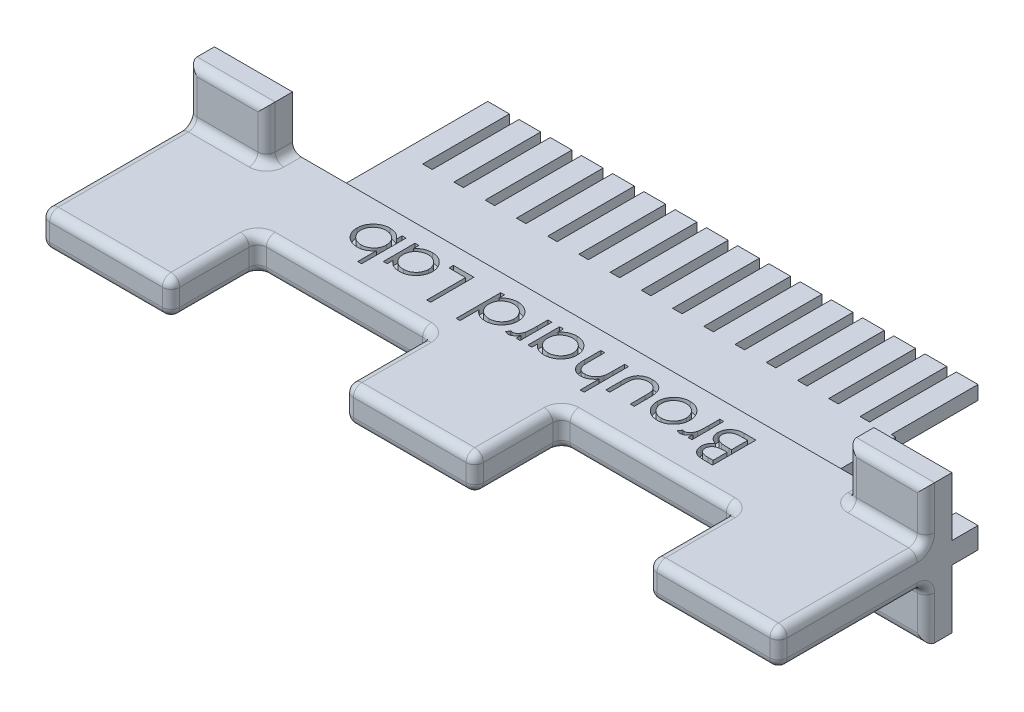
SolidWorks part; units mm, degrees
ref_plane "Front Plane" through (0, 0, 0) normal (0, 0, 1) x (1, 0, 0)
ref_plane "Top Plane" through (0, 0, 0) normal (0, 1, 0) x (1, 0, 0)
ref_plane "Right Plane" through (0, 0, 0) normal (1, 0, 0) x (0, 0, -1)
sketch "Sketch1" plane through (0, 0, 0) normal (0, 0, 1) x (1, 0, 0)
  line L1 (-42.5, 2) -> (42.5, 2)
  line L2 (-42.5, 2) -> (-42.5, -2)
  line L3 (-42.5, -2) -> (42.5, -2)
  line L4 (42.5, 2) -> (42.5, -2)
  line L5 (-42.5, 2) -> (42.5, -2) construction
  line L6 (-42.5, -2) -> (42.5, 2) construction
  point P0 (0, 0)
  dimension "D1" = 85
  dimension "D2" = 4
extrude "Boss-Extrude1" add sketch "Sketch1" along normal blind 10
sketch "Sketch2" plane through (0, 0, 10) normal (0, 0, 1) x (1, 0, 0)
  line L0 (-42.5, -2) -> (42.5, -2) construction
  line L1 (-42.5, 2) -> (-27.5, 2)
  line L2 (-42.5, 2) -> (-42.5, -2)
  line L3 (-42.5, -2) -> (-27.5, -2)
  line L4 (-27.5, 2) -> (-27.5, -2)
  line L6 (42.5, 2) -> (27.5, 2)
  line L7 (42.5, 2) -> (42.5, -2)
  line L8 (42.5, -2) -> (27.5, -2)
  line L9 (27.5, 2) -> (27.5, -2)
  line L10 (-7.5, 2) -> (7.5, 2)
  line L11 (-7.5, 2) -> (-7.5, -2)
  line L12 (-7.5, -2) -> (7.5, -2)
  line L13 (7.5, 2) -> (7.5, -2)
  line L14 (-7.5, 2) -> (7.5, -2) construction
  line L15 (-7.5, -2) -> (7.5, 2) construction
  point P12 (0, 0)
  dimension "D1" = 15
extrude "Boss-Extrude2" add sketch "Sketch2" along normal blind 10
sketch "Sketch3" plane through (0, 0, 0) normal (0, 0, -1) x (-1, 0, 0)
  line L9 (42.5, -1.225) -> (39.95, -1.225)
  line L10 (42.5, -1.225) -> (42.5, 1.225)
  line L11 (42.5, 1.225) -> (39.95, 1.225)
  line L12 (39.95, -1.225) -> (39.95, 1.225)
  line L13 (42.5, -1.225) -> (39.95, 1.225) construction
  line L14 (42.5, 1.225) -> (39.95, -1.225) construction
  line L15 (42.5, 2) -> (42.5, -2) construction
  line L16 (0, 0) -> (0, 13.9589)
  line L17 (-42.5, 1.225) -> (-39.95, -1.225) construction
  line L18 (-42.5, -1.225) -> (-39.95, 1.225) construction
  line L19 (-39.95, -1.225) -> (-39.95, 1.225)
  line L20 (-42.5, 1.225) -> (-39.95, 1.225)
  line L21 (-42.5, -1.225) -> (-42.5, 1.225)
  line L22 (-42.5, -1.225) -> (-39.95, -1.225)
  point P3 (42.5, 0)
  point P10 (41.225, 0)
  point P16 (-41.225, 0)
  line M3 (-42.5, 2) -> (-42.5, -2)
  dimension "D1" = 2.45
  dimension "D2" = 2.55
extrude "Boss-Extrude3" add sketch "Sketch3" along normal blind 3 contours L22 L19 L20 M3 | L12 L11 L10 L9
sketch "Sketch4" plane through (0, 0, 0) normal (0, 0, -1) x (-1, 0, 0)
  line L1 (28.5, -0.8) -> (-28.5, -0.8)
  line L2 (28.5, -0.8) -> (28.5, 0.8)
  line L3 (28.5, 0.8) -> (-28.5, 0.8)
  line L4 (-28.5, -0.8) -> (-28.5, 0.8)
  line L5 (28.5, -0.8) -> (-28.5, 0.8) construction
  line L6 (28.5, 0.8) -> (-28.5, -0.8) construction
  point P0 (0, 0)
  dimension "D1" = 1.6
  dimension "D2" = 57
extrude "Boss-Extrude4" add sketch "Sketch4" along normal blind 7.5
sketch "Sketch6" plane through (0, 0, 0) normal (0, 0, -1) x (-1, 0, 0)
  line L1 (42.5, -2) -> (33.5, -2)
  line L2 (42.5, -2) -> (42.5, -8)
  line L3 (42.5, -8) -> (33.5, -8)
  line L4 (33.5, -2) -> (33.5, -8)
  line L5 (42.5, 2) -> (33.5, 2)
  line L6 (42.5, 2) -> (42.5, 8)
  line L7 (42.5, 8) -> (33.5, 8)
  line L8 (33.5, 2) -> (33.5, 8)
  line L9 (-42.5, -2) -> (-33.5, -2)
  line L10 (-42.5, -2) -> (-42.5, -8)
  line L11 (-42.5, -8) -> (-33.5, -8)
  line L12 (-33.5, -2) -> (-33.5, -8)
  line L13 (-42.5, 2) -> (-33.5, 2)
  line L14 (-42.5, 2) -> (-42.5, 8)
  line L15 (-42.5, 8) -> (-33.5, 8)
  line L16 (-33.5, 2) -> (-33.5, 8)
  dimension "D1" = 6
  dimension "D2" = 9
extrude "Boss-Extrude6" add sketch "Sketch6" against normal blind 3
fillet "Fillet1" radius 1 52 edges at (-42.5, -2, 11.5) (-33.5, -2, 1.5) (-38, -2, 3) (-33.5, -5, 3) (-38, -8, 3) (-42.5, -5, 3) (-27.5, 0, 20) (-35, -2, 20) (-42.5, 0, 20) (-35, 2, 20) (33.5, -2, 1.5) (42.5, -2, 11.5) (42.5, 2, 11.5) (33.5, 2, 1.5) (-33.5, 2, 1.5) (-42.5, 2, 11.5) (38, -8, 3) (33.5, -5, 3) (38, -2, 3) (42.5, -5, 3) (35, -2, 20) (27.5, 0, 20) (35, 2, 20) (42.5, 0, 20) (38, 2, 3) (33.5, 5, 3) (38, 8, 3) (42.5, 5, 3) (0, -2, 20) (-7.5, 0, 20) (0, 2, 20) (7.5, 0, 20) (-38, 8, 3) (-33.5, 5, 3) (-38, 2, 3) (-42.5, 5, 3) (27.5, 2, 15) (27.5, -2, 15) (27.5, 0, 10) (17.5, -2, 10) (17.5, 2, 10) (7.5, -2, 15) (7.5, 2, 15) (7.5, 0, 10) (-7.5, 2, 15) (-7.5, -2, 15) (-27.5, -2, 15) (-27.5, 2, 15) (-27.5, 0, 10) (-17.5, 2, 10) (-7.5, 0, 10) (-17.5, -2, 10)
ref_plane "Plane1" through (0, 0, 0) normal (0, 1, 0) x (1, 0, 0)
sketch "Sketch7" plane through (0, 2, 0) normal (0, 1, 0) x (1, 0, 0)
  line L0 (30.9142, -2.045) -> (-30.9142, -2.045)
  line L1 (32.5, 0) -> (-32.5, 0) construction
  point P2 (0, -2.045)
  point P5 (0, 0)
sketch "Sketch8" plane through (0, 2, 0) normal (0, 1, 0) x (1, 0, 0)
  text T0 "Brouhard Lab" font "Century Gothic" height 5
extrude "Cut-Extrude1" cut sketch "Sketch8" against normal blind 1
sketch "Sketch5" plane through (0, 0, -7.5) normal (0, 0, -1) x (-1, 0, 0)
  line L0 (28.5, 0.8) -> (-28.5, 0.8) construction
  line L1 (28.5, -0.8) -> (26, -0.8)
  line L2 (28.5, -0.8) -> (28.5, 0.8)
  line L3 (28.5, 0.8) -> (26, 0.8)
  line L4 (26, -0.8) -> (26, 0.8)
  line L97 (24.9, -0.8) -> (22.4, -0.8)
  line L98 (24.9, -0.8) -> (24.9, 0.8)
  line L99 (24.9, 0.8) -> (22.4, 0.8)
  line L100 (22.4, -0.8) -> (22.4, 0.8)
  line L101 (21.3, -0.8) -> (18.8, -0.8)
  line L102 (21.3, -0.8) -> (21.3, 0.8)
  line L103 (21.3, 0.8) -> (18.8, 0.8)
  line L104 (18.8, -0.8) -> (18.8, 0.8)
  line L105 (17.7, -0.8) -> (15.2, -0.8)
  line L106 (17.7, -0.8) -> (17.7, 0.8)
  line L107 (17.7, 0.8) -> (15.2, 0.8)
  line L108 (15.2, -0.8) -> (15.2, 0.8)
  line L109 (14.1, -0.8) -> (11.6, -0.8)
  line L110 (14.1, -0.8) -> (14.1, 0.8)
  line L111 (14.1, 0.8) -> (11.6, 0.8)
  line L112 (11.6, -0.8) -> (11.6, 0.8)
  line L113 (10.5, -0.8) -> (8, -0.8)
  line L114 (10.5, -0.8) -> (10.5, 0.8)
  line L115 (10.5, 0.8) -> (8, 0.8)
  line L116 (8, -0.8) -> (8, 0.8)
  line L117 (6.9, -0.8) -> (4.4, -0.8)
  line L118 (6.9, -0.8) -> (6.9, 0.8)
  line L119 (6.9, 0.8) -> (4.4, 0.8)
  line L120 (4.4, -0.8) -> (4.4, 0.8)
  line L121 (3.3, -0.8) -> (0.8, -0.8)
  line L122 (3.3, -0.8) -> (3.3, 0.8)
  line L123 (3.3, 0.8) -> (0.8, 0.8)
  line L124 (0.8, -0.8) -> (0.8, 0.8)
  line L125 (-0.3, -0.8) -> (-2.8, -0.8)
  line L126 (-0.3, -0.8) -> (-0.3, 0.8)
  line L127 (-0.3, 0.8) -> (-2.8, 0.8)
  line L128 (-2.8, -0.8) -> (-2.8, 0.8)
  line L129 (-3.9, -0.8) -> (-6.4, -0.8)
  line L130 (-3.9, -0.8) -> (-3.9, 0.8)
  line L131 (-3.9, 0.8) -> (-6.4, 0.8)
  line L132 (-6.4, -0.8) -> (-6.4, 0.8)
  line L133 (-7.5, -0.8) -> (-10, -0.8)
  line L134 (-7.5, -0.8) -> (-7.5, 0.8)
  line L135 (-7.5, 0.8) -> (-10, 0.8)
  line L136 (-10, -0.8) -> (-10, 0.8)
  line L137 (-11.1, -0.8) -> (-13.6, -0.8)
  line L138 (-11.1, -0.8) -> (-11.1, 0.8)
  line L139 (-11.1, 0.8) -> (-13.6, 0.8)
  line L140 (-13.6, -0.8) -> (-13.6, 0.8)
  line L141 (-14.7, -0.8) -> (-17.2, -0.8)
  line L142 (-14.7, -0.8) -> (-14.7, 0.8)
  line L143 (-14.7, 0.8) -> (-17.2, 0.8)
  line L144 (-17.2, -0.8) -> (-17.2, 0.8)
  line L145 (-18.3, -0.8) -> (-20.8, -0.8)
  line L146 (-18.3, -0.8) -> (-18.3, 0.8)
  line L147 (-18.3, 0.8) -> (-20.8, 0.8)
  line L148 (-20.8, -0.8) -> (-20.8, 0.8)
  line L149 (-21.9, -0.8) -> (-24.4, -0.8)
  line L150 (-21.9, -0.8) -> (-21.9, 0.8)
  line L151 (-21.9, 0.8) -> (-24.4, 0.8)
  line L152 (-24.4, -0.8) -> (-24.4, 0.8)
  line L153 (-25.5, -0.8) -> (-28, -0.8)
  line L154 (-25.5, -0.8) -> (-25.5, 0.8)
  line L155 (-25.5, 0.8) -> (-28, 0.8)
  line L156 (-28, -0.8) -> (-28, 0.8)
  dimension "D2" = 2.5
  dimension "D1" = 16
extrude "Boss-Extrude5" add sketch "Sketch5" along normal blind 10
